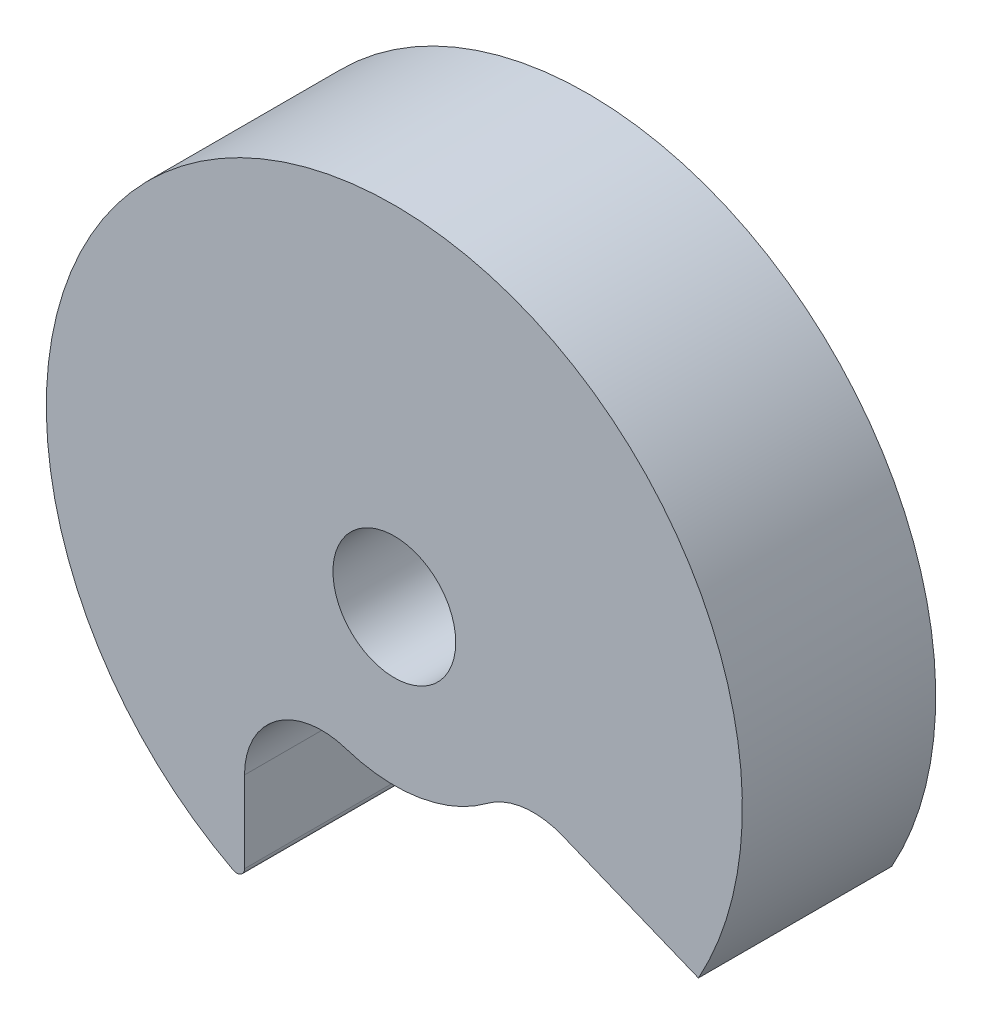
SolidWorks part; units mm, degrees
ref_plane "Front Plane" through (0, 0, 0) normal (0, 0, 1) x (1, 0, 0)
ref_plane "Top Plane" through (0, 0, 0) normal (0, 1, 0) x (1, 0, 0)
ref_plane "Right Plane" through (0, 0, 0) normal (1, 0, 0) x (0, 0, -1)
sketch "Sketch2" plane through (0, 0, 0) normal (0, 0, 1) x (1, 0, 0)
  circle A3 centre (-0.2846, 9.3309) radius 1.5875
  circle A23 centre (-0.2846, 9.3309) radius 9
  dimension "D1" = 3.175
  dimension "D2" = 18
extrude "Boss-Extrude2" add sketch "Sketch2" along normal blind 5
sketch "Sketch3" plane through (0, 0, 5) normal (0, 0, 1) x (1, 0, 0)
  line L0 (-4.1588, 1.2075) -> (-4.1588, 3.6312)
  line L1 (7.5785, 4.9525) -> (4.0642, 6.3806)
  circle A0 centre (-0.2846, 9.3309) radius 9 construction
  arc A1 (-1.5341, 5.5311) -> (2.1126, 6.1289) centre (-0.2846, 9.3309) ccw
  arc A2 (-4.1588, 1.2075) -> (7.5785, 4.9525) centre (-0.2846, 9.3309) ccw
  arc A3 (4.0642, 6.3806) -> (2.1126, 6.1289) centre (3.3112, 4.5278) ccw
  arc A4 (-4.1588, 3.6312) -> (-1.5341, 5.5311) centre (-2.1588, 3.6312) cw
  point P5 (7.0786, 4.1557)
  point P13 (0, 0)
  point P14 (0, 0)
  point P15 (1.3576, 5.7322)
  point P16 (6.3712, 3.2729)
  point P17 (2.6334, 5.4305)
  point P18 (6.0413, 2.9291)
  point P19 (2.7283, 5.4776)
  point P20 (5.7305, 2.6362)
  point P21 (3.3712, 5.5311)
  point P22 (3.7558, 5.8858)
  point P23 (4.0642, 6.3806)
  dimension "D1" = 4
  dimension "D2" = 2
extrude "Cut-Extrude1" cut sketch "Sketch3" against normal through all
fillet "Fillet1" radius 0.2 1 edges at (-4.1588, 1.2075, 2.5)
